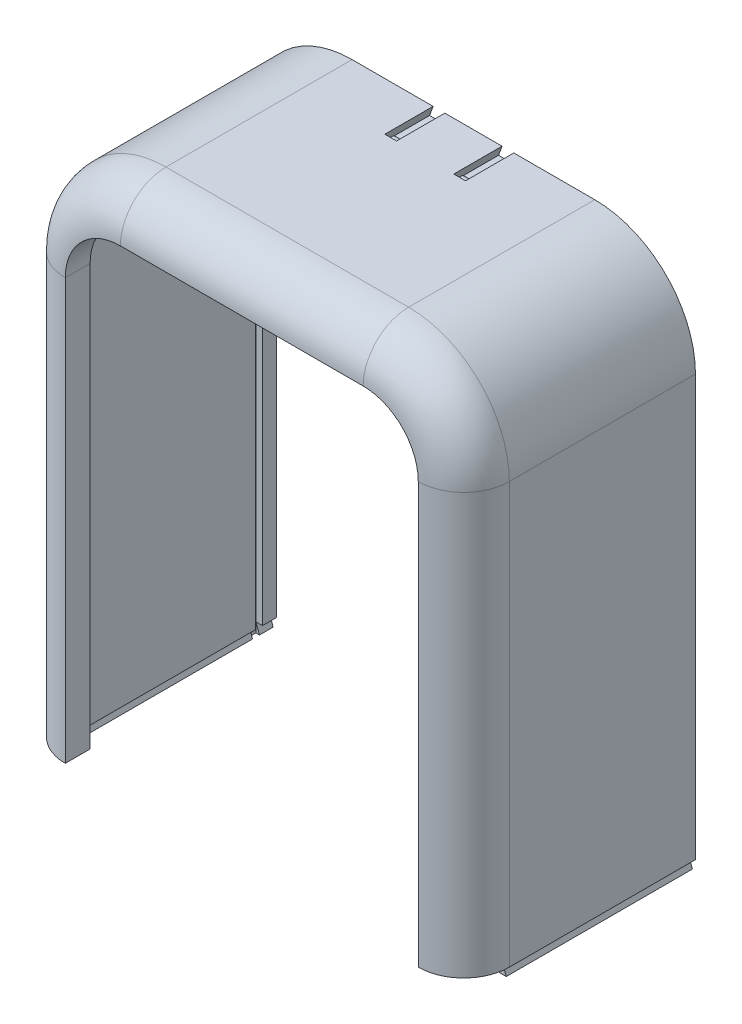
SolidWorks part; units mm, degrees
ref_plane "前基準面" through (0, 0, 0) normal (0, 0, 1) x (1, 0, 0)
ref_plane "上基準面" through (0, 0, 0) normal (0, 1, 0) x (1, 0, 0)
ref_plane "右基準面" through (0, 0, 0) normal (1, 0, 0) x (0, 0, -1)
sketch "草圖1" plane through (0, 0, 0) normal (0, 0, 1) x (1, 0, 0)
  line L0 (0, 36.9915) -> (0, -45.4073) construction
  line L1 (-32.2, 25) -> (-32.2, -36)
  line L2 (-17.6, 36) -> (17.6, 36)
  line L3 (-28.6, 25) -> (-28.6, -36)
  line L5 (28.6, 25) -> (28.6, -36)
  line L6 (-28.6, 36) -> (28.6, -36) construction
  line L7 (-28.6, -36) -> (28.6, 36) construction
  line L8 (-17.6, 39.6) -> (17.6, 39.6)
  line L9 (32.2, 25) -> (32.2, -36)
  line L11 (-32.2, -36) -> (-31.25, -36)
  line L12 (28.6, -36) -> (29.55, -36)
  line L13 (-32.2, -39.6) -> (32.2, -39.6) construction
  line L14 (-28.6, -36) -> (28.6, -36) construction
  line L15 (32.2, 25) -> (32.2, -39.6) construction
  line L16 (-32.2, 25) -> (-32.2, -39.6) construction
  line L17 (-30.4, -33.8886) -> (-30.4, -38.1902) construction
  line L18 (-31.25, -36) -> (-31.7596, -37.4)
  line L19 (-31.7596, -37.4) -> (-29.0404, -37.4)
  line L20 (-29.55, -36) -> (-29.0404, -37.4)
  line L21 (-29.55, -36) -> (-28.6, -36)
  line L22 (29.55, -36) -> (29.0404, -37.4)
  line L23 (31.7596, -37.4) -> (29.0404, -37.4)
  line L24 (31.25, -36) -> (31.7596, -37.4)
  line L25 (31.25, -36) -> (32.2, -36)
  arc A0 (-17.6, 36) -> (-28.6, 25) centre (-17.6, 25) ccw
  arc A1 (28.6, 25) -> (17.6, 36) centre (17.6, 25) ccw
  arc A2 (-17.6, 39.6) -> (-32.2, 25) centre (-17.6, 25) ccw
  arc A3 (32.2, 25) -> (17.6, 39.6) centre (17.6, 25) ccw
  point P3 (0, 0)
  point P31 (-30.4, -37.4)
  dimension "D3" = 11
  dimension "D1" = 57.2
  dimension "D2" = 72
  dimension "D5" = 70
  dimension "D6" = 1.4
  dimension "D7" = 0.95
  dimension "D4" = 3.6
extrude "填料-伸長1" add sketch "草圖1" along normal blind 27
ref_plane "平面1" through (0, 0, 0) normal (0, 0, 1) x (1, 0, 0)
ref_plane "平面2" through (0, 0, 3) normal (0, 0, 1) x (1, 0, 0)
sketch "草圖4" plane through (0, 0, 3) normal (0, 0, 1) x (1, 0, 0)
  line L1 (-28.6, -36) -> (-28.6, 25)
  line L3 (28.6, 25) -> (28.6, -36)
  line L5 (-17.6, 36) -> (17.6, 36)
  line L6 (29.56, 25) -> (29.56, -36)
  line L7 (-29.56, -36) -> (-29.56, 25)
  line L8 (-17.6, 36.96) -> (17.6, 36.96)
  line L9 (29.56, 25) -> (29.56, -36)
  line L10 (-29.56, -36) -> (-29.56, 25)
  line L11 (-17.6, 36.96) -> (17.6, 36.96)
  line L12 (-29.56, -36) -> (-29.56, -37.4)
  line L13 (-31.7596, -37.4) -> (-29.0404, -37.4) construction
  line L14 (-29.56, -37.4) -> (-28.6, -37.4)
  line L15 (-28.6, -37.4) -> (-28.6, -36)
  line L16 (29.56, -36) -> (29.56, -37.4)
  line L17 (29.56, -37.4) -> (28.6, -37.4)
  line L18 (28.6, -37.4) -> (28.6, -36)
  line L19 (23.7903, 25) -> (33.4203, 25) construction
  arc A0 (-28.6, 25) -> (-17.6, 36) centre (-17.6, 25) cw
  arc A1 (17.6, 36) -> (28.6, 25) centre (17.6, 25) cw
  arc A4 (29.56, 25) -> (17.6, 36.96) centre (17.6, 25) ccw
  arc A5 (-17.6, 36.96) -> (-29.56, 25) centre (-17.6, 25) ccw
  arc A6 (29.56, 25) -> (17.6, 36.96) centre (17.6, 25) ccw
  arc A7 (-17.6, 36.96) -> (-29.56, 25) centre (-17.6, 25) ccw
  dimension "D1" = 0.96
extrude "除料-伸長1" cut sketch "草圖4" against normal blind 1
sketch "草圖5" plane through (0, 0, 27) normal (0, 0, 1) x (1, 0, 0)
  line L0 (-30.4, -36) -> (-30.4, 25)
  line L1 (-35.7212, 25) -> (-18.4815, 25) construction
  line L2 (-17.6, 37.8) -> (17.6, 37.8)
  line L3 (-17.6, 42.3693) -> (-17.6, 21.8353) construction
  line L4 (0, -29.9923) -> (0, 71.7202) construction
  line L5 (17.6, 39.6) -> (-17.6, 39.6) construction
  line L6 (30.4, -36) -> (30.4, 25)
  arc A0 (-17.6, 37.8) -> (-30.4, 25) centre (-17.6, 25) ccw
  arc A1 (17.6, 37.8) -> (30.4, 25) centre (17.6, 25) cw
  point P14 (0, 37.8)
  dimension "D1" = 1.8
sketch "草圖6" plane through (0, -37.4, 0) normal (0, -1, 0) x (1, 0, 0)
  line L1 (30.4, 27) -> (17.6, 27) construction
  line L3 (-28.6, 27) -> (-32.2, 27)
  line L4 (-25.6, 30) -> (-25.6, 33.6)
  arc A0 (-25.6, 30) -> (-28.6, 27) centre (-25.6, 27) ccw
  arc A1 (-25.6, 33.6) -> (-32.2, 27) centre (-25.6, 27) ccw
  dimension "D2" = 3
sketch "草圖7" plane through (0, -36, 0) normal (0, -1, 0) x (1, 0, 0)
  line L3 (-28.6, 27) -> (-32.2, 27)
  line L4 (-25.6, 30) -> (-25.6, 33.6)
  arc A0 (-25.6, 30) -> (-28.6, 27) centre (-25.6, 27) ccw
  arc A1 (-25.6, 33.6) -> (-32.2, 27) centre (-25.6, 27) ccw
sweep "掃出2" add profiles "草圖7" path "草圖5"
sketch "草圖9" plane through (0, 0, 0) normal (0, 0, -1) x (-1, 0, 0)
  line L0 (0, 51.4045) -> (0, -14.5803) construction
  line L1 (-5.85, 39.6) -> (-6.3596, 38.2)
  line L2 (-17.6, 39.6) -> (17.6, 39.6) construction
  line L3 (-6.3596, 38.2) -> (-3.6404, 38.2)
  line L4 (-4.15, 39.6) -> (-3.6404, 38.2)
  line L5 (-5, 42.7101) -> (-5, 33.2765) construction
  line L6 (-5.85, 39.6) -> (-4.15, 39.6)
  line L7 (5, 42.7101) -> (5, 33.2765) construction
  line L8 (5.85, 39.6) -> (4.15, 39.6)
  line L9 (4.15, 39.6) -> (3.6404, 38.2)
  line L10 (6.3596, 38.2) -> (3.6404, 38.2)
  line L11 (5.85, 39.6) -> (6.3596, 38.2)
  point P8 (-5, 39.6)
  point P13 (-5, 38.2)
  point P19 (5, 38.2)
  point P20 (5, 39.6)
  dimension "D1" = 70
  dimension "D2" = 1.4
  dimension "D3" = 0.85
  dimension "D4" = 10
extrude "除料-伸長4" cut sketch "草圖9" against normal blind 7
sketch "草圖10" plane through (0, 0, 0) normal (1, 0, 0) x (0, 0, -1)
  line L0 (-7, 38.2) -> (0, 38.2) construction
  line L2 (-5.9, 38.2) -> (-5.1, 38.2)
  line L4 (-5.5, 40.4089) -> (-5.5, 35.7958) construction
  line L5 (0, 35.42) -> (0, -35.42) construction
  arc A1 (-5.9, 38.2) -> (-5.1, 38.2) centre (-5.5, 37.6732) cw
  dimension "D2" = 0.8
  dimension "D1" = 5.5
extrude "填料-伸長2" add sketch "草圖10" along normal mid plane 13
